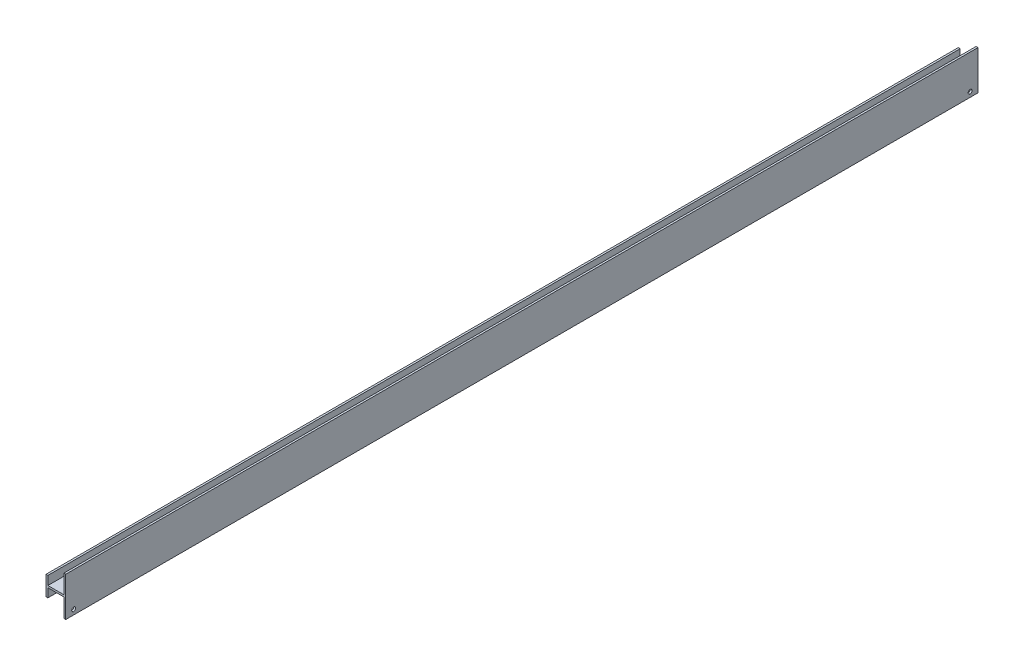
SolidWorks part; units mm, degrees
material "6061 Alloy"
ref_plane "Front Plane" through (0, 0, 0) normal (0, 0, 1) x (1, 0, 0)
ref_plane "Top Plane" through (0, 0, 0) normal (0, 1, 0) x (1, 0, 0)
ref_plane "Right Plane" through (0, 0, 0) normal (1, 0, 0) x (0, 0, -1)
sketch "Sketch1" plane through (0, 0, 0) normal (0, 0, 1) x (1, 0, 0)
  line L0 (58.674, 15.6718) -> (58.674, -15.6718)
  line L1 (42.926, 7.7851) -> (42.926, -7.7851)
  line L2 (44.45, -0.762) -> (57.15, -0.762)
  line L3 (57.15, -15.6718) -> (57.15, -0.762)
  line L4 (44.45, -7.7851) -> (44.45, -0.762)
  line L5 (58.674, -15.6718) -> (57.15, -15.6718)
  line L6 (42.926, -7.7851) -> (44.45, -7.7851)
  line L7 (44.45, 0.762) -> (57.15, 0.762)
  line L8 (44.45, 7.7851) -> (44.45, 0.762)
  line L9 (57.15, 15.6718) -> (57.15, 0.762)
  line L10 (58.674, 15.6718) -> (57.15, 15.6718)
  line L11 (42.926, 7.7851) -> (44.45, 7.7851)
extrude "Extrude1" add sketch "Sketch1" along normal mid plane 728.6625
sketch "Sketch2" plane through (57.15, 0, 0) normal (-1, 0, 0) x (0, 0, 1)
  line L0 (364.3313, -15.6718) -> (364.3313, -7.7851) construction
  line L1 (364.3313, -11.7285) -> (357.9812, -11.7285) construction
  line L2 (-364.3313, -15.6718) -> (-364.3313, -7.7851) construction
  line L3 (-364.3313, -11.7285) -> (-357.9812, -11.7285) construction
  circle A0 centre (357.9812, -11.7285) radius 1.5875
  circle A1 centre (-357.9812, -11.7285) radius 1.5875
extrude "Cut-Extrude1" cut sketch "Sketch2" against normal up to surface (1.524 mm away) up to face at (58.674, 0, 0)
